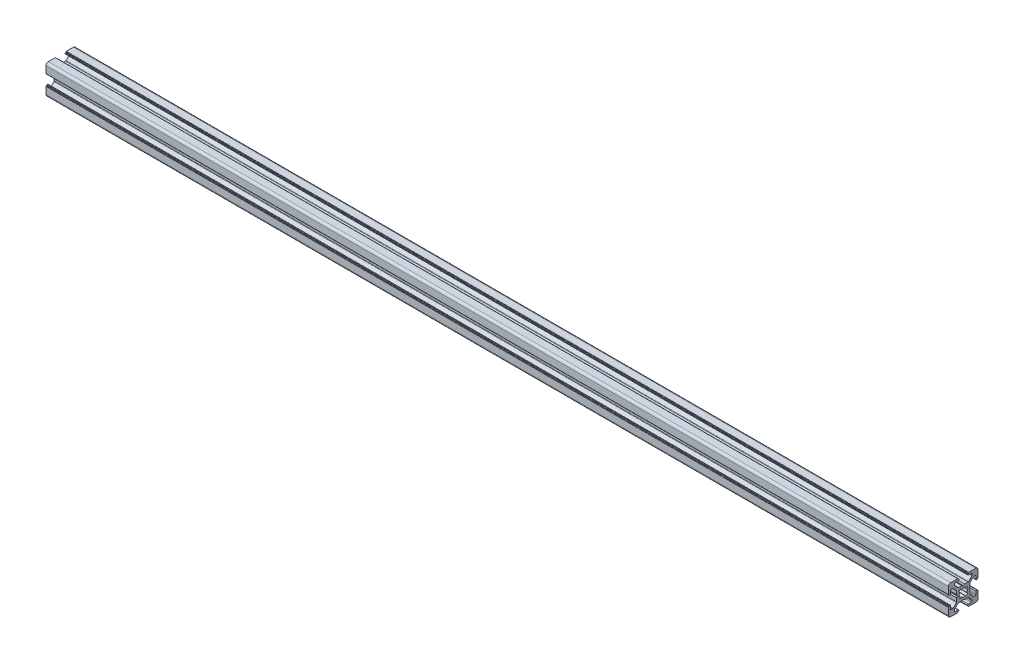
SolidWorks part; units mm, degrees
material "1060 Alloy"
ref_plane "Front Plane" through (0, 0, 0) normal (0, 0, 1) x (1, 0, 0)
ref_plane "Top Plane" through (0, 0, 0) normal (0, 1, 0) x (1, 0, 0)
ref_plane "Right Plane" through (0, 0, 0) normal (1, 0, 0) x (0, 0, -1)
sketch "Sketch1" plane through (0, 0, 0) normal (0, 0, 1) x (1, 0, 0)
  line L0 (0, 0) -> (611, 0)
  dimension "D1" = 611
other "T-slot 20X20(1)"
ref_plane "Plane1" through (0, 0, 0) normal (1, 0, 0) x (0, 1, 0)
sketch "Sketch11" plane through (0, 0, 0) normal (1, 0, 0) x (0, 1, 0)
  line L0 (2.9914, 1.9095) -> (2.4445, 1.2578)
  line L1 (2.4445, -1.2578) -> (2.9914, -1.9095)
  line L2 (1.9134, -2.9889) -> (1.2578, -2.4445)
  line L3 (-1.2578, -2.4445) -> (-1.9135, -2.9889)
  line L4 (-2.9914, -1.9095) -> (-2.4445, -1.2578)
  line L5 (-2.4445, 1.2578) -> (-2.9914, 1.9095)
  line L6 (-1.9134, 2.9889) -> (-1.2578, 2.4445)
  line L7 (1.2577, 2.4446) -> (1.9134, 2.9889)
  line L8 (5.4998, -8.4985) -> (3.4998, -8.4985)
  line L9 (2.9998, -8.9985) -> (2.9998, -9.2985)
  line L10 (3.1998, -9.4985) -> (3.3489, -9.4985)
  line L11 (3.5489, -9.6985) -> (3.5489, -9.7989)
  line L12 (3.7489, -9.9989) -> (8.5002, -9.9989)
  line L13 (10.0002, -8.4989) -> (10.0002, -3.7489)
  line L14 (9.8002, -3.5489) -> (9.6994, -3.5489)
  line L15 (9.4994, -3.3489) -> (9.4994, -3.1985)
  line L16 (9.2994, -2.9985) -> (8.9994, -2.9985)
  line L17 (8.4994, -3.4985) -> (8.4994, -5.4986)
  line L18 (7.9994, -5.9986) -> (7.2672, -5.9986)
  line L19 (6.9136, -5.8521) -> (4.6458, -3.5844)
  line L20 (4.4994, -3.2308) -> (4.4994, -0.9522)
  line L21 (4.4726, -0.8522) -> (4.0375, -0.0986)
  line L22 (4.0375, 0.1014) -> (4.4726, 0.855)
  line L23 (4.4994, 0.955) -> (4.4994, 3.2333)
  line L24 (4.6458, 3.5869) -> (6.9136, 5.8546)
  line L25 (7.2672, 6.0011) -> (7.9994, 6.0011)
  line L26 (8.4994, 5.5011) -> (8.4994, 3.5007)
  line L27 (8.9994, 3.0007) -> (9.2994, 3.0007)
  line L28 (9.4994, 3.2007) -> (9.4994, 3.3489)
  line L29 (9.6994, 3.5489) -> (9.8002, 3.5489)
  line L30 (10.0002, 3.7489) -> (10.0002, 8.4989)
  line L31 (8.5002, 9.9989) -> (3.7489, 9.9989)
  line L32 (3.5489, 9.7989) -> (3.5489, 9.7011)
  line L33 (3.3489, 9.5011) -> (3.1998, 9.5011)
  line L34 (2.9998, 9.3011) -> (2.9998, 9.0011)
  line L35 (3.4998, 8.5011) -> (5.4998, 8.5011)
  line L36 (5.9998, 8.0011) -> (5.9998, 7.2692)
  line L37 (5.8533, 6.9156) -> (3.5852, 4.6475)
  line L38 (3.2317, 4.5011) -> (0.953, 4.5011)
  line L39 (0.853, 4.4743) -> (0.0994, 4.0392)
  line L40 (-0.1006, 4.0392) -> (-0.8542, 4.4743)
  line L41 (-0.9542, 4.5011) -> (-3.2325, 4.5011)
  line L42 (-3.586, 4.6475) -> (-5.8541, 6.9157)
  line L43 (-6.0006, 7.2692) -> (-6.0006, 8.0011)
  line L44 (-5.5006, 8.5011) -> (-3.5002, 8.5011)
  line L45 (-3.0002, 9.0011) -> (-3.0002, 9.3011)
  line L46 (-3.2002, 9.5011) -> (-3.3489, 9.5011)
  line L47 (-3.5489, 9.7011) -> (-3.5489, 9.7989)
  line L48 (-3.7489, 9.9989) -> (-8.4985, 9.9989)
  line L49 (-9.9985, 8.4989) -> (-9.9985, 3.7489)
  line L50 (-9.7985, 3.5489) -> (-9.6999, 3.5489)
  line L51 (-9.4999, 3.3489) -> (-9.4999, 3.2007)
  line L52 (-9.2999, 3.0007) -> (-8.9999, 3.0007)
  line L53 (-8.4999, 3.5007) -> (-8.4999, 5.5011)
  line L54 (-7.9999, 6.0011) -> (-7.2679, 6.0011)
  line L55 (-6.9144, 5.8546) -> (-4.6467, 3.5869)
  line L56 (-4.5003, 3.2334) -> (-4.5003, 0.955)
  line L57 (-4.4735, 0.855) -> (-4.0384, 0.1014)
  line L58 (-4.0384, -0.0986) -> (-4.4735, -0.8522)
  line L59 (-4.5003, -0.9522) -> (-4.5003, -3.2308)
  line L60 (-4.6467, -3.5844) -> (-6.9145, -5.8521)
  line L61 (-7.268, -5.9986) -> (-7.9999, -5.9986)
  line L62 (-8.4999, -5.4986) -> (-8.4999, -3.4985)
  line L63 (-8.9999, -2.9985) -> (-9.2999, -2.9985)
  line L64 (-9.4999, -3.1985) -> (-9.4999, -3.3489)
  line L65 (-9.6999, -3.5489) -> (-9.7985, -3.5489)
  line L66 (-9.9985, -3.7489) -> (-9.9985, -8.4989)
  line L67 (-8.4985, -9.9989) -> (-3.7489, -9.9989)
  line L68 (-3.5489, -9.7989) -> (-3.5489, -9.6985)
  line L69 (-3.3489, -9.4985) -> (-3.2002, -9.4985)
  line L70 (-3.0002, -9.2985) -> (-3.0002, -8.9985)
  line L71 (-3.5002, -8.4985) -> (-5.5006, -8.4985)
  line L72 (-6.0006, -7.9985) -> (-6.0006, -7.2667)
  line L73 (-5.8541, -6.9131) -> (-3.5864, -4.6454)
  line L74 (-3.2328, -4.4989) -> (-0.9542, -4.4989)
  line L75 (-0.8542, -4.4721) -> (-0.1006, -4.037)
  line L76 (0.0994, -4.037) -> (0.853, -4.4721)
  line L77 (0.953, -4.4989) -> (3.232, -4.4989)
  line L78 (3.5856, -4.6454) -> (5.8533, -6.9131)
  line L79 (5.9998, -7.2667) -> (5.9998, -7.9985)
  arc A0 (2.4445, 1.2578) -> (2.4445, -1.2578) centre (0, 0) cw
  arc A1 (2.9914, -1.9095) -> (1.9134, -2.9889) centre (0, 0) cw
  arc A2 (1.2578, -2.4445) -> (-1.2578, -2.4445) centre (0, 0) cw
  arc A3 (-1.9135, -2.9889) -> (-2.9914, -1.9095) centre (0, 0) cw
  arc A4 (-2.4445, -1.2578) -> (-2.4445, 1.2578) centre (0, 0) cw
  arc A5 (-2.9914, 1.9095) -> (-1.9134, 2.9889) centre (0, 0) cw
  arc A6 (-1.2578, 2.4445) -> (1.2577, 2.4446) centre (0, 0) cw
  arc A7 (1.9134, 2.9889) -> (2.9914, 1.9095) centre (0, 0) cw
  arc A8 (5.9998, -7.9985) -> (5.4998, -8.4985) centre (5.4998, -7.9985) cw
  arc A9 (3.4998, -8.4985) -> (2.9998, -8.9985) centre (3.4998, -8.9985) ccw
  arc A10 (2.9998, -9.2985) -> (3.1998, -9.4985) centre (3.1998, -9.2985) ccw
  arc A11 (3.3489, -9.4985) -> (3.5489, -9.6985) centre (3.3489, -9.6985) cw
  arc A12 (3.5489, -9.7989) -> (3.7489, -9.9989) centre (3.7489, -9.7989) ccw
  arc A13 (8.5002, -9.9989) -> (10.0002, -8.4989) centre (8.5002, -8.4989) ccw
  arc A14 (10.0002, -3.7489) -> (9.8002, -3.5489) centre (9.8002, -3.7489) ccw
  arc A15 (9.6994, -3.5489) -> (9.4994, -3.3489) centre (9.6994, -3.3489) cw
  arc A16 (9.4994, -3.1985) -> (9.2994, -2.9985) centre (9.2994, -3.1985) ccw
  arc A17 (8.9994, -2.9985) -> (8.4994, -3.4985) centre (8.9994, -3.4985) ccw
  arc A18 (8.4994, -5.4986) -> (7.9994, -5.9986) centre (7.9994, -5.4986) cw
  arc A19 (7.2672, -5.9986) -> (6.9136, -5.8521) centre (7.2672, -5.4986) cw
  arc A20 (4.6458, -3.5844) -> (4.4994, -3.2308) centre (4.9994, -3.2308) cw
  arc A21 (4.4994, -0.9522) -> (4.4726, -0.8522) centre (4.2994, -0.9522) ccw
  arc A22 (4.0375, -0.0986) -> (4.0375, 0.1014) centre (4.2107, 0.0014) cw
  arc A23 (4.4726, 0.855) -> (4.4994, 0.955) centre (4.2994, 0.955) ccw
  arc A24 (4.4994, 3.2333) -> (4.6458, 3.5869) centre (4.9994, 3.2333) cw
  arc A25 (6.9136, 5.8546) -> (7.2672, 6.0011) centre (7.2672, 5.5011) cw
  arc A26 (7.9994, 6.0011) -> (8.4994, 5.5011) centre (7.9994, 5.5011) cw
  arc A27 (8.4994, 3.5007) -> (8.9994, 3.0007) centre (8.9994, 3.5007) ccw
  arc A28 (9.2994, 3.0007) -> (9.4994, 3.2007) centre (9.2994, 3.2007) ccw
  arc A29 (9.4994, 3.3489) -> (9.6994, 3.5489) centre (9.6994, 3.3489) cw
  arc A30 (9.8002, 3.5489) -> (10.0002, 3.7489) centre (9.8002, 3.7489) ccw
  arc A31 (10.0002, 8.4989) -> (8.5002, 9.9989) centre (8.5002, 8.4989) ccw
  arc A32 (3.7489, 9.9989) -> (3.5489, 9.7989) centre (3.7489, 9.7989) ccw
  arc A33 (3.5489, 9.7011) -> (3.3489, 9.5011) centre (3.3489, 9.7011) cw
  arc A34 (3.1998, 9.5011) -> (2.9998, 9.3011) centre (3.1998, 9.3011) ccw
  arc A35 (2.9998, 9.0011) -> (3.4998, 8.5011) centre (3.4998, 9.0011) ccw
  arc A36 (5.4998, 8.5011) -> (5.9998, 8.0011) centre (5.4998, 8.0011) cw
  arc A37 (5.9998, 7.2692) -> (5.8533, 6.9156) centre (5.4998, 7.2692) cw
  arc A38 (3.5852, 4.6475) -> (3.2317, 4.5011) centre (3.2317, 5.0011) cw
  arc A39 (0.953, 4.5011) -> (0.853, 4.4743) centre (0.953, 4.3011) ccw
  arc A40 (0.0994, 4.0392) -> (-0.1006, 4.0392) centre (-0.0006, 4.2124) cw
  arc A41 (-0.8542, 4.4743) -> (-0.9542, 4.5011) centre (-0.9542, 4.3011) ccw
  arc A42 (-3.2325, 4.5011) -> (-3.586, 4.6475) centre (-3.2325, 5.0011) cw
  arc A43 (-5.8541, 6.9157) -> (-6.0006, 7.2692) centre (-5.5006, 7.2692) cw
  arc A44 (-6.0006, 8.0011) -> (-5.5006, 8.5011) centre (-5.5006, 8.0011) cw
  arc A45 (-3.5002, 8.5011) -> (-3.0002, 9.0011) centre (-3.5002, 9.0011) ccw
  arc A46 (-3.0002, 9.3011) -> (-3.2002, 9.5011) centre (-3.2002, 9.3011) ccw
  arc A47 (-3.3489, 9.5011) -> (-3.5489, 9.7011) centre (-3.3489, 9.7011) cw
  arc A48 (-3.5489, 9.7989) -> (-3.7489, 9.9989) centre (-3.7489, 9.7989) ccw
  arc A49 (-8.4985, 9.9989) -> (-9.9985, 8.4989) centre (-8.4985, 8.4989) ccw
  arc A50 (-9.9985, 3.7489) -> (-9.7985, 3.5489) centre (-9.7985, 3.7489) ccw
  arc A51 (-9.6999, 3.5489) -> (-9.4999, 3.3489) centre (-9.6999, 3.3489) cw
  arc A52 (-9.4999, 3.2007) -> (-9.2999, 3.0007) centre (-9.2999, 3.2007) ccw
  arc A53 (-8.9999, 3.0007) -> (-8.4999, 3.5007) centre (-8.9999, 3.5007) ccw
  arc A54 (-8.4999, 5.5011) -> (-7.9999, 6.0011) centre (-7.9999, 5.5011) cw
  arc A55 (-7.2679, 6.0011) -> (-6.9144, 5.8546) centre (-7.2679, 5.5011) cw
  arc A56 (-4.6467, 3.5869) -> (-4.5003, 3.2334) centre (-5.0003, 3.2334) cw
  arc A57 (-4.5003, 0.955) -> (-4.4735, 0.855) centre (-4.3003, 0.955) ccw
  arc A58 (-4.0384, 0.1014) -> (-4.0384, -0.0986) centre (-4.2116, 0.0014) cw
  arc A59 (-4.4735, -0.8522) -> (-4.5003, -0.9522) centre (-4.3003, -0.9522) ccw
  arc A60 (-4.5003, -3.2308) -> (-4.6467, -3.5844) centre (-5.0003, -3.2308) cw
  arc A61 (-6.9145, -5.8521) -> (-7.268, -5.9986) centre (-7.268, -5.4986) cw
  arc A62 (-7.9999, -5.9986) -> (-8.4999, -5.4986) centre (-7.9999, -5.4986) cw
  arc A63 (-8.4999, -3.4985) -> (-8.9999, -2.9985) centre (-8.9999, -3.4985) ccw
  arc A64 (-9.2999, -2.9985) -> (-9.4999, -3.1985) centre (-9.2999, -3.1985) ccw
  arc A65 (-9.4999, -3.3489) -> (-9.6999, -3.5489) centre (-9.6999, -3.3489) cw
  arc A66 (-9.7985, -3.5489) -> (-9.9985, -3.7489) centre (-9.7985, -3.7489) ccw
  arc A67 (-9.9985, -8.4989) -> (-8.4985, -9.9989) centre (-8.4985, -8.4989) ccw
  arc A68 (-3.7489, -9.9989) -> (-3.5489, -9.7989) centre (-3.7489, -9.7989) ccw
  arc A69 (-3.5489, -9.6985) -> (-3.3489, -9.4985) centre (-3.3489, -9.6985) cw
  arc A70 (-3.2002, -9.4985) -> (-3.0002, -9.2985) centre (-3.2002, -9.2985) ccw
  arc A71 (-3.0002, -8.9985) -> (-3.5002, -8.4985) centre (-3.5002, -8.9985) ccw
  arc A72 (-5.5006, -8.4985) -> (-6.0006, -7.9985) centre (-5.5006, -7.9985) cw
  arc A73 (-6.0006, -7.2667) -> (-5.8541, -6.9131) centre (-5.5006, -7.2667) cw
  arc A74 (-3.5864, -4.6454) -> (-3.2328, -4.4989) centre (-3.2328, -4.9989) cw
  arc A75 (-0.9542, -4.4989) -> (-0.8542, -4.4721) centre (-0.9542, -4.2989) ccw
  arc A76 (-0.1006, -4.037) -> (0.0994, -4.037) centre (-0.0006, -4.2102) cw
  arc A77 (0.853, -4.4721) -> (0.953, -4.4989) centre (0.953, -4.2989) ccw
  arc A78 (3.232, -4.4989) -> (3.5856, -4.6454) centre (3.232, -4.9989) cw
  arc A79 (5.8533, -6.9131) -> (5.9998, -7.2667) centre (5.4998, -7.2667) cw
  point P233 (0, 0)
